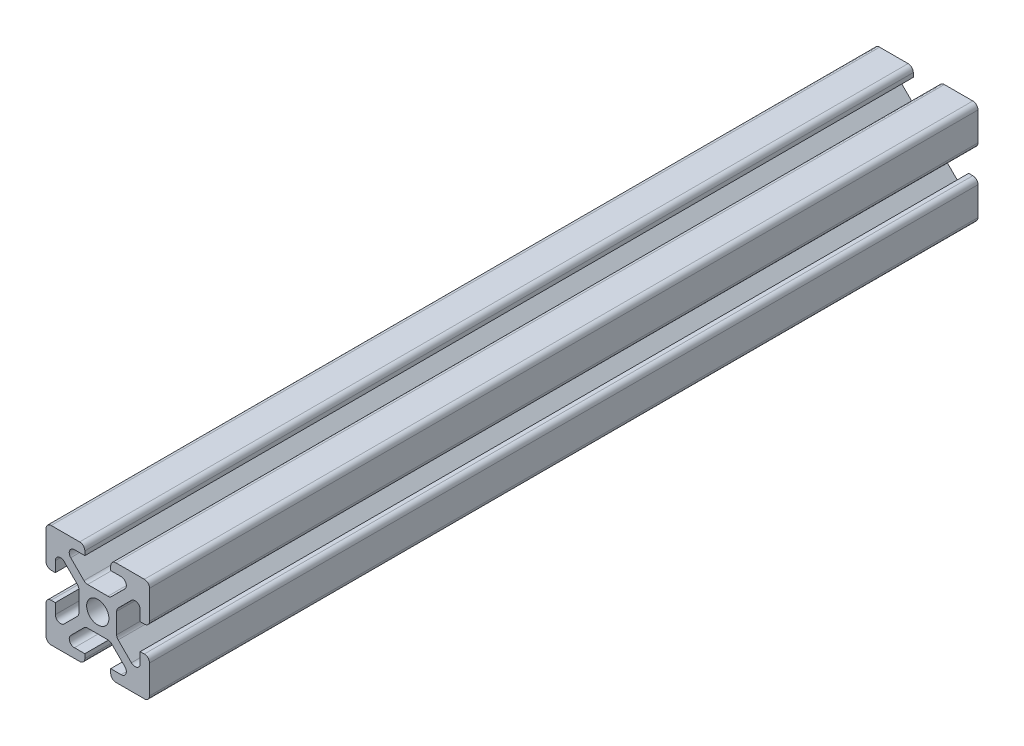
SolidWorks part; units mm, degrees
ref_plane "Piano frontale" through (0, 0, 0) normal (0, 0, 1) x (1, 0, 0)
ref_plane "Piano superiore" through (0, 0, 0) normal (0, 1, 0) x (1, 0, 0)
ref_plane "Piano destro" through (0, 0, 0) normal (1, 0, 0) x (0, 0, -1)
ref_plane "Piano1" through (0, 0, 0) normal (0, 0, -1) x (-1, 0, 0)
sketch "Schizzo1" plane through (0, 0, 0) normal (0, 0, -1) x (-1, 0, 0)
  line L0 (8.2, 2.5) -> (9, 2.5)
  line L1 (10, 3.5) -> (10, 9)
  line L2 (9, 10) -> (3.5, 10)
  line L3 (2.5, 9) -> (2.5, 8.2)
  line L4 (2.5, 8.2) -> (4.513, 8.2)
  line L5 (5.2201, 6.4929) -> (2.6701, 3.9429)
  line L6 (1.963, 3.65) -> (-1.963, 3.65)
  line L7 (-2.6701, 3.9429) -> (-5.2201, 6.4929)
  line L8 (-4.513, 8.2) -> (-2.5, 8.2)
  line L9 (-2.5, 8.2) -> (-2.5, 9)
  line L10 (-3.5, 10) -> (-9, 10)
  line L11 (-10, 9) -> (-10, 3.5)
  line L12 (-9, 2.5) -> (-8.2, 2.5)
  line L13 (-8.2, 2.5) -> (-8.2, 4.513)
  line L14 (-6.4929, 5.2201) -> (-3.9429, 2.6701)
  line L15 (-3.65, 1.963) -> (-3.65, -1.963)
  line L16 (-3.9429, -2.6701) -> (-6.4929, -5.2201)
  line L17 (-8.2, -4.513) -> (-8.2, -2.5)
  line L18 (-8.2, -2.5) -> (-9, -2.5)
  line L19 (-10, -3.5) -> (-10, -9)
  line L20 (-9, -10) -> (-3.5, -10)
  line L21 (-2.5, -9) -> (-2.5, -8.2)
  line L22 (-2.5, -8.2) -> (-4.513, -8.2)
  line L23 (-5.2201, -6.4929) -> (-2.6701, -3.9429)
  line L24 (-1.963, -3.65) -> (1.963, -3.65)
  line L25 (2.6701, -3.9429) -> (5.2201, -6.4929)
  line L26 (4.513, -8.2) -> (2.5, -8.2)
  line L27 (2.5, -8.2) -> (2.5, -9)
  line L28 (3.5, -10) -> (9, -10)
  line L29 (10, -9) -> (10, -3.5)
  line L30 (9, -2.5) -> (8.2, -2.5)
  line L31 (8.2, -2.5) -> (8.2, -4.513)
  line L32 (6.4929, -5.2201) -> (3.9429, -2.6701)
  line L33 (3.65, -1.963) -> (3.65, 1.963)
  line L34 (3.9429, 2.6701) -> (6.4929, 5.2201)
  line L35 (8.2, 4.513) -> (8.2, 2.5)
  circle A0 centre (0, 0) radius 2.15
  arc A1 (9, 2.5) -> (10, 3.5) centre (9, 3.5) ccw
  arc A2 (10, 9) -> (9, 10) centre (9, 9) ccw
  arc A3 (3.5, 10) -> (2.5, 9) centre (3.5, 9) ccw
  arc A4 (4.513, 8.2) -> (5.2201, 6.4929) centre (4.513, 7.2) cw
  arc A5 (2.6701, 3.9429) -> (1.963, 3.65) centre (1.963, 4.65) cw
  arc A6 (-1.963, 3.65) -> (-2.6701, 3.9429) centre (-1.963, 4.65) cw
  arc A7 (-5.2201, 6.4929) -> (-4.513, 8.2) centre (-4.513, 7.2) cw
  arc A8 (-2.5, 9) -> (-3.5, 10) centre (-3.5, 9) ccw
  arc A9 (-9, 10) -> (-10, 9) centre (-9, 9) ccw
  arc A10 (-10, 3.5) -> (-9, 2.5) centre (-9, 3.5) ccw
  arc A11 (-8.2, 4.513) -> (-6.4929, 5.2201) centre (-7.2, 4.513) cw
  arc A12 (-3.9429, 2.6701) -> (-3.65, 1.963) centre (-4.65, 1.963) cw
  arc A13 (-3.65, -1.963) -> (-3.9429, -2.6701) centre (-4.65, -1.963) cw
  arc A14 (-6.4929, -5.2201) -> (-8.2, -4.513) centre (-7.2, -4.513) cw
  arc A15 (-9, -2.5) -> (-10, -3.5) centre (-9, -3.5) ccw
  arc A16 (-10, -9) -> (-9, -10) centre (-9, -9) ccw
  arc A17 (-3.5, -10) -> (-2.5, -9) centre (-3.5, -9) ccw
  arc A18 (-4.513, -8.2) -> (-5.2201, -6.4929) centre (-4.513, -7.2) cw
  arc A19 (-2.6701, -3.9429) -> (-1.963, -3.65) centre (-1.963, -4.65) cw
  arc A20 (1.963, -3.65) -> (2.6701, -3.9429) centre (1.963, -4.65) cw
  arc A21 (5.2201, -6.4929) -> (4.513, -8.2) centre (4.513, -7.2) cw
  arc A22 (2.5, -9) -> (3.5, -10) centre (3.5, -9) ccw
  arc A23 (9, -10) -> (10, -9) centre (9, -9) ccw
  arc A24 (10, -3.5) -> (9, -2.5) centre (9, -3.5) ccw
  arc A25 (8.2, -4.513) -> (6.4929, -5.2201) centre (7.2, -4.513) cw
  arc A26 (3.9429, -2.6701) -> (3.65, -1.963) centre (4.65, -1.963) cw
  arc A27 (3.65, 1.963) -> (3.9429, 2.6701) centre (4.65, 1.963) cw
  arc A28 (6.4929, 5.2201) -> (8.2, 4.513) centre (7.2, 4.513) cw
  point P94 (0, 3.65)
  point P95 (3.65, 0)
extrude "Estrusione-Estrusione1" add sketch "Schizzo1" against normal blind 160
